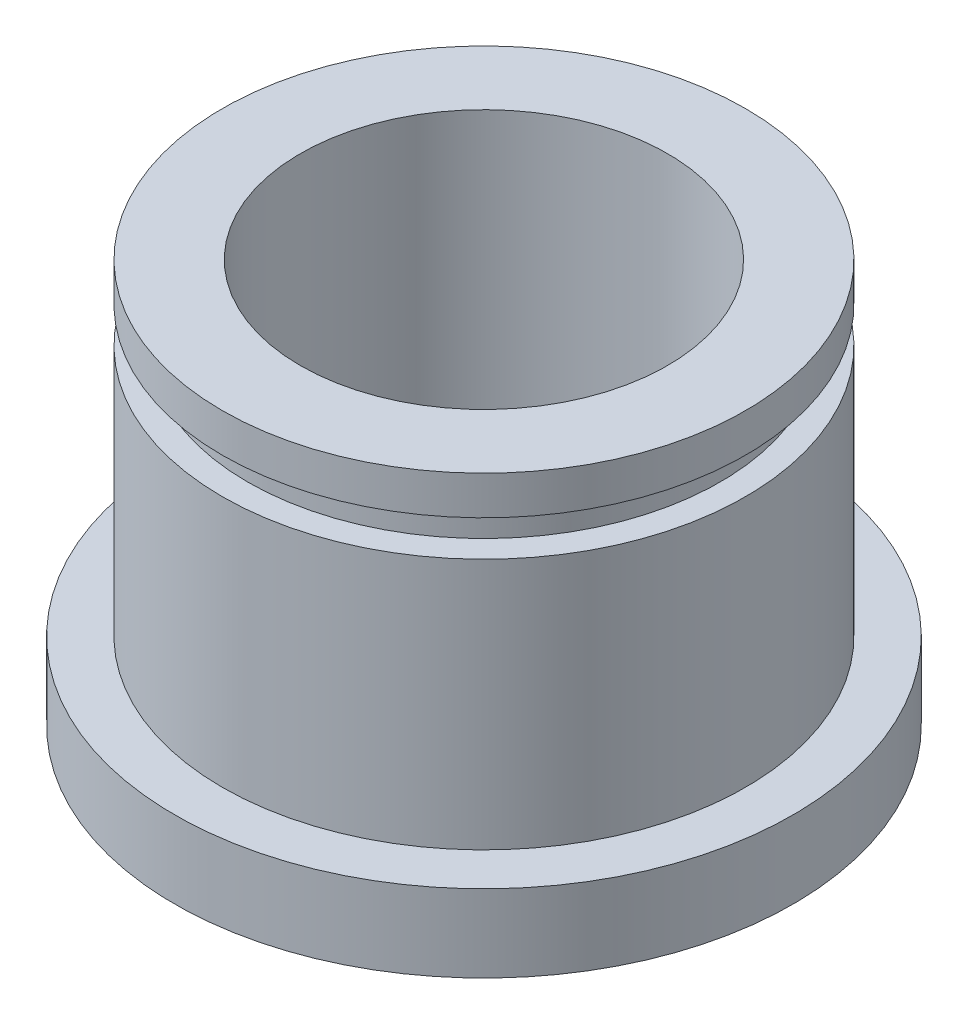
SolidWorks part; units mm, degrees
material "7075-T6 (SN)"
ref_plane "X-Y Datum" through (0, 0, 0) normal (0, 0, 1) x (1, 0, 0)
ref_plane "X-Z Datum" through (0, 0, 0) normal (0, 1, 0) x (1, 0, 0)
ref_plane "Y-Z Datum" through (0, 0, 0) normal (1, 0, 0) x (0, 0, -1)
sketch "Sketch1" plane through (0, 0, 0) normal (1, 0, 0) x (0, 0, -1)
  line L0 (0, 0) -> (0, 8253.6099) construction
  line L1 (0, -4.1434) -> (-6.35, -4.1434)
  line L2 (-6.35, -4.1434) -> (-6.35, -2.5559)
  line L3 (-6.35, -2.5559) -> (-5.3721, -2.5559)
  line L4 (-5.3721, -2.5559) -> (-5.3721, 2.613)
  line L7 (-4.8514, 3.3496) -> (-5.3721, 3.3496)
  line L8 (-5.3721, 3.3496) -> (-5.3721, 4.1434)
  line L9 (-5.3721, 4.1434) -> (0, 4.1434)
  line L10 (0, 4.1434) -> (0, -4.1434)
  line L11 (0, 0) -> (-50000, 0) construction
  line L12 (-5.3721, 2.613) -> (-4.8514, 2.613)
  line L13 (-4.8514, 2.613) -> (-4.8514, 3.3496)
  point P9 (0, 0)
  dimension "D1" = 12.7
  dimension "D2" = 10.7442
  dimension "D3" = 1.5875
  dimension "D4" = 9.7028
  dimension "D5" = 0.7937
  dimension "D6" = 5.1689
  dimension "D7" = 0.7366
revolve "Revolve1" add sketch "Sketch1" angle 360 about L0
hole_wizard "19/64 (0.29688) Diameter Hole1" positions "Sketch2" profile "Sketch3" hole size "19/64" standard "ANSI Inch"
sketch "Sketch2" plane through (0, 4.1434, 0) normal (0, 1, 0) x (1, 0, 0)
  point P0 (0, 0)
sketch "Sketch3" plane through (0, 4.1434, 0) normal (1, 0, 0) x (0, 0, 1)
  line L0 (0, 0) -> (0, 10.6475)
  line L1 (0, 10.6475) -> (3.7704, 8.382)
  line L2 (3.7704, 8.382) -> (3.7704, 0)
  line L5 (3.7704, 0) -> (0, 0)
  line L10 (0, 10.6475) -> (-3.7704, 8.382) construction
  line L11 (0, -6.35) -> (0, 107.95) construction
  dimension "Hole Dia." = 7.5408
  dimension "Hole Depth" = 8.382
  dimension "Drill Angle" = 118
chamfer "Chamfer1" distance 0.7937 angle 45 1 edges at (0, -4.1434, 3.7704)
